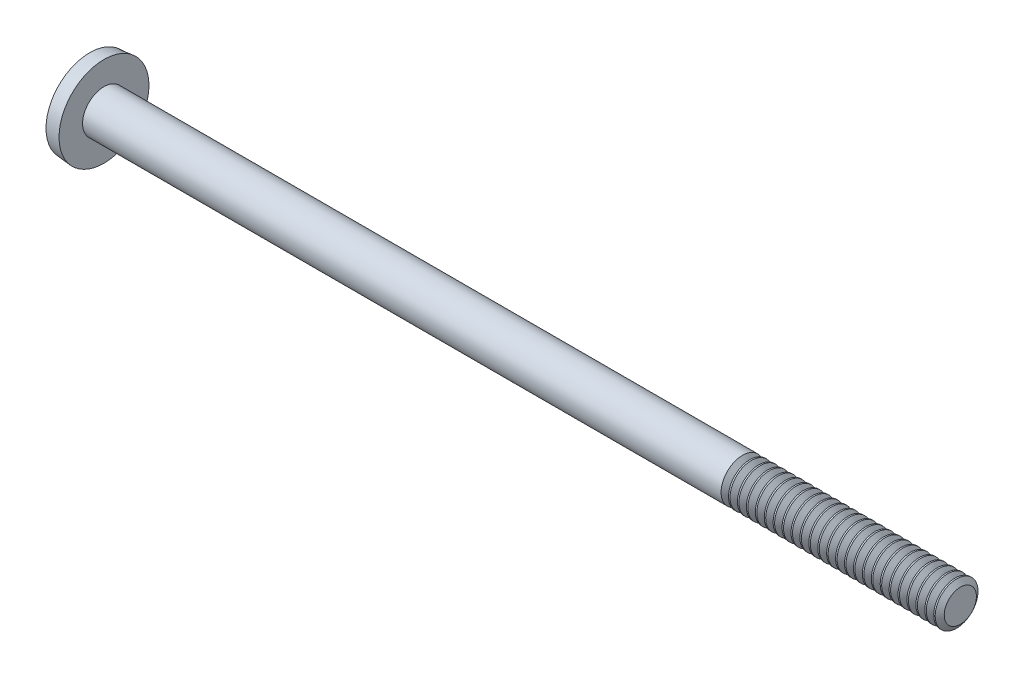
SolidWorks part; units mm, degrees
ref_plane "Plane1" through (0, 0, 0) normal (0, 0, 1) x (1, 0, 0)
ref_plane "Plane2" through (0, 0, 0) normal (0, 1, 0) x (1, 0, 0)
ref_plane "Plane3" through (0, 0, 0) normal (1, 0, 0) x (0, 0, -1)
sketch "BodySke" plane through (0, 0, 0) normal (0, 0, 1) x (1, 0, 0)
  line L0 (0.8128, 0.762) -> (0.8128, 1.6002)
  line L1 (0.8128, 1.6002) -> (0.3048, 1.5558)
  line L2 (-25.4, 0) -> (127, 0) construction
  line L3 (0.8128, -1.6002) -> (0.3048, -1.5558) construction
  line L4 (0.8128, 0.762) -> (31.2928, 0.762)
  line L5 (31.2928, 0.762) -> (31.2928, 0)
  line L6 (31.2928, 0) -> (0, 0)
  line L7 (0.8128, -0.762) -> (31.2928, -0.762) construction
  line L8 (1.1303, 6.35) -> (1.1303, -3.175) construction
  line L9 (23.6728, 6.35) -> (23.6728, -3.175) construction
  arc A0 (0, 0) -> (0.3048, 1.5558) centre (4.1228, 0) cw
  dimension "Head_ang" = 85
revolve "Base-Revolve" add sketch "BodySke" angle 360 about L2
cosmetic thread "ThreadCosmetic" [suppressed] parameters "Thread_length"=7.62, "Thread_minor"=1.1455
sketch "Sketch2" plane through (0, 0, 0) normal (1, 0, 0) x (0, 0, -1)
  line L0 (1.6002, -0.2921) -> (1.6002, 0.2921)
  line L1 (1.6002, 0.2921) -> (-1.6002, 0.2921)
  line L2 (-1.6002, 0.2921) -> (-1.6002, -0.2921)
  line L3 (-1.6002, -0.2921) -> (1.6002, -0.2921)
extrude "Slot" [suppressed] cut sketch "Sketch2" along normal blind 0.4572
sketch "Sketch3" plane through (0, 0, 0) normal (1, 0, 0) x (0, 0, -1)
  line L0 (-0.2921, 1.0541) -> (0.2921, 1.0541)
  line L1 (0.2921, 1.0541) -> (0.2921, -1.0541)
  line L2 (0.2921, -1.0541) -> (-0.2921, -1.0541)
  line L3 (-0.2921, -1.0541) -> (-0.2921, 1.0541)
  dimension "D1" = 0.2921
ref_plane "Plane4" through (1.0668, 0, 0) normal (1, 0, 0) x (0, 0, -1)
sketch "Sketch4" plane through (1.0668, 0, 0) normal (1, 0, 0) x (0, 0, -1)
  line L0 (-0.1461, 0.1461) -> (0.1461, 0.1461)
  line L1 (0.1461, 0.1461) -> (0.1461, -0.1461)
  line L2 (0.1461, -0.1461) -> (-0.1461, -0.1461)
  line L3 (-0.1461, -0.1461) -> (-0.1461, 0.1461)
  dimension "D1" = 0.2921
  dimension "D2" = 0.1461
  dimension "D3" = 0.2921
  dimension "D4" = 0.1461
loft "Cross" cut profiles "Sketch3", "Sketch4"
pattern_circular "CirPattern1" count 2 every 90 about axis through (0, 0, 0) along (1, 0, 0) of "Cross"
sketch "ThdSchSke" plane through (0, 0, 0) normal (0, 0, 1) x (1, 0, 0)
  line L0 (23.6728, -0.5728) -> (23.5403, -0.762)
  line L1 (23.6728, -0.5728) -> (23.8053, -0.762)
  line L2 (23.8053, -0.762) -> (23.8053, -0.9525)
  line L3 (-3.175, 0) -> (5.1513, 0) construction
  line L5 (23.8053, -0.9525) -> (23.5403, -0.9525)
  line L6 (23.5403, -0.9525) -> (23.5403, -0.762)
  dimension "SideAngle" = 55
  dimension "VeeAngle" = 70
revolve "ThreadSchematic" cut sketch "ThdSchSke" angle 360 about L3
pattern_linear "ThdSchPat" count 25 spacing 0.3175 along (1, 0, 0) of "ThreadSchematic"
equation "\"D1@Sketch3\" = \"Cross_width@Sketch3\" / 2"
equation "\"D2@Sketch3\" = \"Cross_dia@Sketch3\" / 2"
equation "\"D1@Sketch4\" = \"Cross_width@Sketch3\"*.5"
equation "\"D2@Sketch4\" = \"D1@Sketch4\" / 2"
equation "\"D3@Sketch4\" = \"D1@Sketch4\""
equation "\"D4@Sketch4\" = \"D2@Sketch4\""
equation "\"D1@Sketch2\" = \"Head_dia@BodySke\""
equation "\"D2@Sketch2\" = \"D1@Sketch2\" / 2"
equation "\"D3@Sketch2\" = \"Slot_width@Sketch2\" / 2"
equation "\"Thread_length@ThreadCosmetic\" = ((sgn( (\"Length@BodySke\" - \"Advance@BodySke\" ) - \"Thread_nom@BodySke\" )-1)*( (\"Length@BodySke\" - \"Advance@BodySke\" ) - \"Thread_nom@BodySke\" ))/-2+ \"Thread_nom@BodySke\""
equation "\"Thread_minor@ThdSchSke\" = \"Thread_minor@ThreadCosmetic\""
equation "\"Diameter@ThdSchSke\" = \"Diameter@BodySke\""
equation "\"Overcut@ThdSchSke\" = \"Diameter@BodySke\" * 1.25"
equation "\"Start@ThdSchSke\" = \"Head_ht@BodySke\" + \"Length@BodySke\" - \"Thread_length@ThreadCosmetic\"  '---Non-countersunk---"
equation "\"Num_threads@ThdSchPat\" = int( \"Thread_length@ThreadCosmetic\" / \"Advance@BodySke\" + 0.999 )  + 1"
equation "\"Advance@ThdSchPat\" = \"Thread_length@ThreadCosmetic\" /  (\"Num_threads@ThdSchPat\" - 1) 'relax it"
